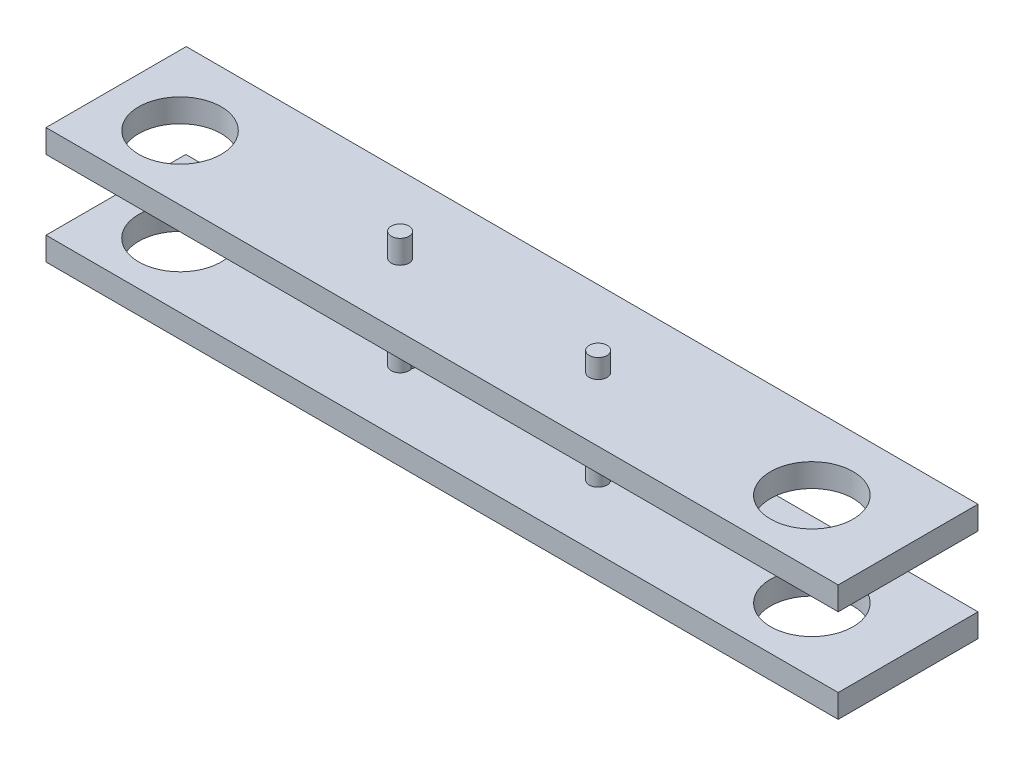
SolidWorks part; units mm, degrees
ref_plane "Alzado" through (0, 0, 0) normal (0, 0, 1) x (1, 0, 0)
ref_plane "Planta" through (0, 0, 0) normal (0, 1, 0) x (1, 0, 0)
ref_plane "Vista lateral" through (0, 0, 0) normal (1, 0, 0) x (0, 0, -1)
sketch "Croquis1" plane through (0, 0, 0) normal (0, 1, 0) x (1, 0, 0)
  line L0 (-107.1961, 0) -> (324.6039, 0)
  line L1 (-107.1961, 0) -> (-107.1961, 76.2)
  line L2 (-107.1961, 76.2) -> (324.6039, 76.2)
  line L3 (324.6039, 76.2) -> (324.6039, 0)
  dimension "D1" = 431.8
  dimension "D2" = 76.2
extrude "Saliente-Extruir2" add sketch "Croquis1" along normal blind 12.7
sketch "Croquis3" plane through (0, 0, 0) normal (0, 1, 0) x (1, 0, 0)
  line L0 (307.7458, 38.1) -> (250.4554, 38.1) construction
  line L1 (250.4554, 38.1) -> (250.4554, 67.4299) construction
  circle A2 centre (-53.9189, 38.1) radius 4.826
  circle A3 centre (51.0178, 38.1) radius 4.826
  dimension "D2" = 9.652
  dimension "D3" = 9.652
extrude "Saliente-Extruir4" add sketch "Croquis3" along normal blind 63.5
sketch "Croquis4" plane through (0, 0, 0) normal (0, 1, 0) x (1, 0, 0)
  circle A0 centre (275.131, 35.1079) radius 22.479
  dimension "D1" = 44.958
extrude "Cortar-Extruir3" cut sketch "Croquis4" along normal blind 219.71
sketch "Croquis6" plane through (0, 0, 0) normal (0, 1, 0) x (1, 0, 0)
  circle A0 centre (275.131, 35.1079) radius 22.479
  dimension "D1" = 44.958
extrude "Cortar-Extruir5" cut sketch "Croquis6" along normal blind 180.594
ref_plane "Plano1" through (0, 50.8, 0) normal (0, 1, 0) x (1, 0, 0)
sketch "Croquis7" plane through (0, 50.8, 0) normal (0, 1, 0) x (1, 0, 0)
  line L0 (-107.1961, 76.4397) -> (324.6039, 76.2)
  line L1 (324.6039, 76.2) -> (324.6039, 0)
  line L2 (324.6039, 0) -> (-107.1961, 0)
  line L3 (-107.1961, 0) -> (-107.1961, 76.4397)
  line L5 (-107.1961, 0) -> (-107.1961, 76.4397)
  dimension "D1" = 431.8
extrude "Saliente-Extruir5" add sketch "Croquis7" along normal blind 12.7 contours L3 L2 L1 L0
sketch "Croquis8" plane through (0, 0, 0) normal (0, -1, 0) x (1, 0, 0)
  circle A0 centre (275.131, -35.1079) radius 22.479
  dimension "D1" = 44.958
extrude "Cortar-Extruir7" cut sketch "Croquis8" against normal blind 115.062 and the other way blind 46.736
sketch "Croquis9" plane through (0, 0, 0) normal (0, 1, 0) x (1, 0, 0)
  circle A0 centre (-69.2561, 35.1079) radius 22.479
  dimension "D1" = 44.958
extrude "Cortar-Extruir8" cut sketch "Croquis9" along normal blind 153.162 and the other way blind 103.886
sketch "Croquis10" plane through (0, 63.5, 0) normal (0, 1, 0) x (1, 0, 0)
  circle A0 centre (158.865, 34.905) radius 4.826
  dimension "D1" = 9.652
extrude "Saliente-Extruir6" add sketch "Croquis10" against normal blind 75.184 and the other way blind 10.414
sketch "Croquis12" plane through (0, 0, 0) normal (0, 1, 0) x (1, 0, 0)
  circle A0 centre (50.915, 34.905) radius 4.826
extrude "Saliente-Extruir7" add sketch "Croquis12" against normal blind 13.208 and the other way blind 76.2
